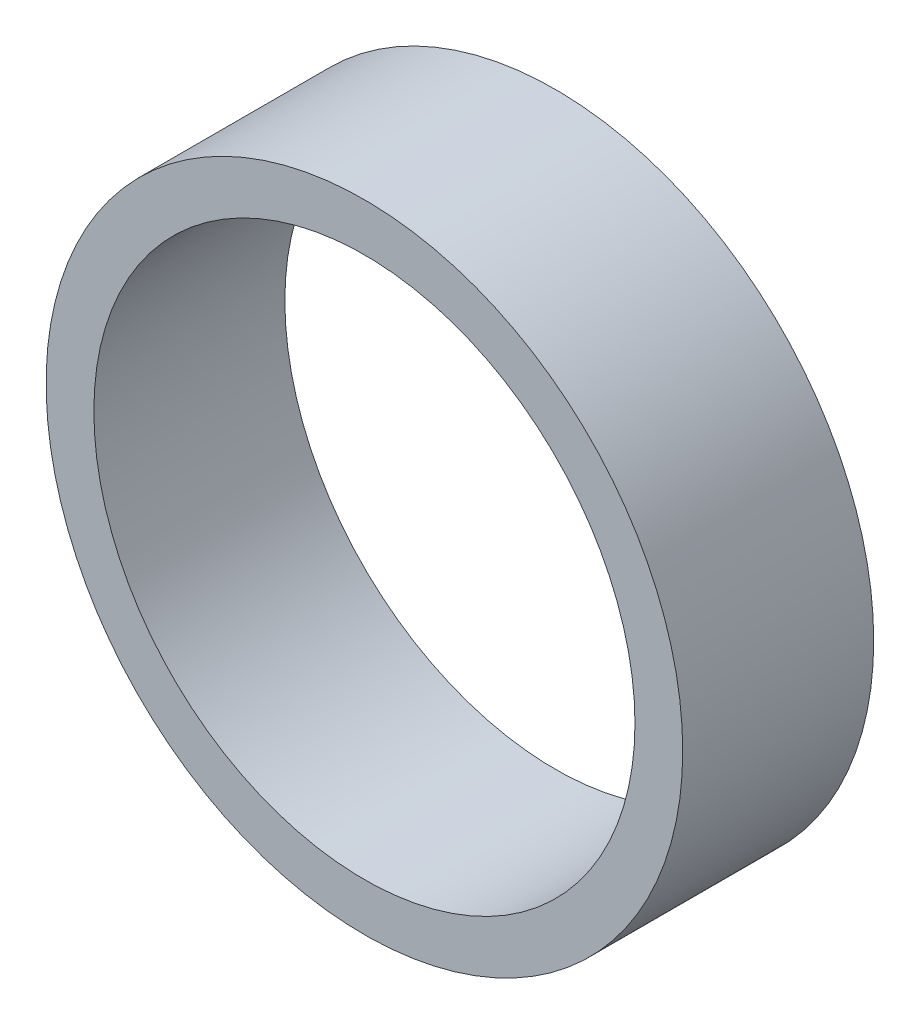
SolidWorks part; units mm, degrees
material "ABS PC"
ref_plane "Front Plane" through (0, 0, 0) normal (0, 0, 1) x (1, 0, 0)
ref_plane "Top Plane" through (0, 0, 0) normal (0, 1, 0) x (1, 0, 0)
ref_plane "Right Plane" through (0, 0, 0) normal (1, 0, 0) x (0, 0, -1)
sketch "Sketch1" plane through (0, 0, 0) normal (0, 0, 1) x (1, 0, 0)
  circle A0 centre (0, 0) radius 10
  circle A1 centre (0, 0) radius 8.5
extrude "Boss-Extrude1" add sketch "Sketch1" along normal blind 6
